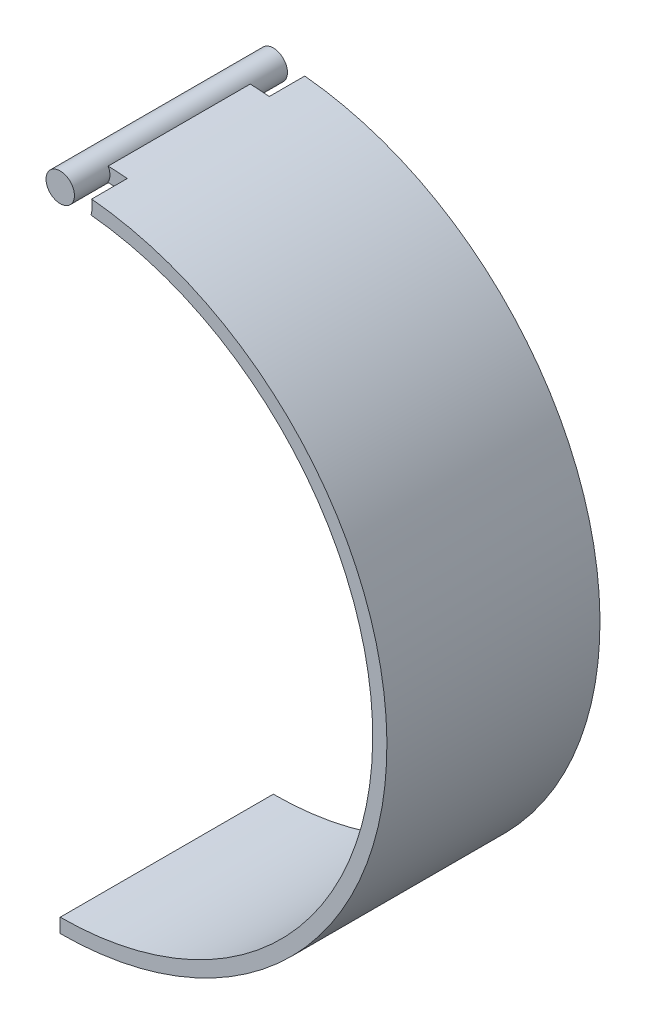
SolidWorks part; units mm, degrees
ref_plane "正面" through (0, 0, 0) normal (0, 0, 1) x (1, 0, 0)
ref_plane "平面" through (0, 0, 0) normal (0, 1, 0) x (1, 0, 0)
ref_plane "右側面" through (0, 0, 0) normal (1, 0, 0) x (0, 0, -1)
sketch "ｽｹｯﾁ1" plane through (0, 0, 0) normal (0, 0, 1) x (1, 0, 0)
  circle A0 centre (0, 0) radius 1
  dimension "D1" = 2
extrude "ﾎﾞｽ - 押し出し1" add sketch "ｽｹｯﾁ1" along normal blind 15
sketch "ｽｹｯﾁ2" plane through (0, 0, 15) normal (0, 0, 1) x (1, 0, 0)
  line L0 (0, -45) -> (0, 0) construction
  line L1 (0, -44.5) -> (0, -45.5)
  line L2 (0, 0.5) -> (0, -0.5)
  arc A0 (0, 0) -> (0, -45) centre (0, -22.5) cw construction
  arc A1 (0, -0.5) -> (0, -44.5) centre (0, -22.5) cw
  arc A2 (0, 0.5) -> (0, -45.5) centre (0, -22.5) cw
  dimension "D2" = 22.5
  dimension "D3" = 1
  dimension "D4" = 0.5
  dimension "D1" = 45
extrude "ﾎﾞｽ - 押し出し2" add sketch "ｽｹｯﾁ2" against normal blind 15
sketch "ｽｹｯﾁ3" plane through (0, 0, 15) normal (0, 0, 1) x (1, 0, 0)
  arc A0 (0.8754, 0.4833) -> (0.8562, -0.5167) centre (0, 0) cw
  arc A1 (0, -44.5) -> (0.8562, -0.5167) centre (0, -22.5) ccw construction
  arc A2 (0.8562, -0.5167) -> (2.1666, -0.6069) centre (0, -22.5) cw
  arc A3 (2.1666, -0.6069) -> (2.2154, 0.3931) centre (0, 0) ccw
  arc A4 (0, -45.5) -> (0.8754, 0.4833) centre (0, -22.5) ccw construction
  arc A5 (0.8754, 0.4833) -> (2.2154, 0.3931) centre (0, -22.5) cw
  dimension "D1" = 2.25
extrude "ｶｯﾄ - 押し出し1" cut sketch "ｽｹｯﾁ3" against normal blind 2.5
sketch "ｽｹｯﾁ4" plane through (0, 0, 0) normal (0, 0, -1) x (-1, 0, 0)
  arc A0 (-0.8754, 0.4833) -> (-0.8562, -0.5167) centre (0, 0) ccw
  arc A1 (-0.8562, -0.5167) -> (-0.8754, 0.4833) centre (0, 0) ccw construction
  arc A2 (-0.8754, 0.4833) -> (-2.2154, 0.3931) centre (0, -22.5) ccw
  arc A3 (-2.2154, 0.3931) -> (-2.1666, -0.6069) centre (0, 0) ccw
  arc A4 (-0.8562, -0.5167) -> (0, -44.5) centre (0, -22.5) ccw construction
  arc A5 (-2.1666, -0.6069) -> (-0.8562, -0.5167) centre (0, -22.5) cw
  dimension "D1" = 2.25
extrude "ｶｯﾄ - 押し出し2" cut sketch "ｽｹｯﾁ4" against normal blind 2.5
sketch "ｽｹｯﾁ5" plane through (0, 0, 0) normal (0, 0, -1) x (-1, 0, 0)
  point P0 (0, 0)
sketch3d "3Dｽｹｯﾁ1"
  line L0 (0, 0, 0) -> (-10, 0, 0)
  line L1 (0, 0, 0) -> (0, -10, 0)
  line L2 (0, 0, 0) -> (0, 0, 10)
  dimension "D1" = 10
  dimension "D2" = 10
  dimension "D3" = 10
